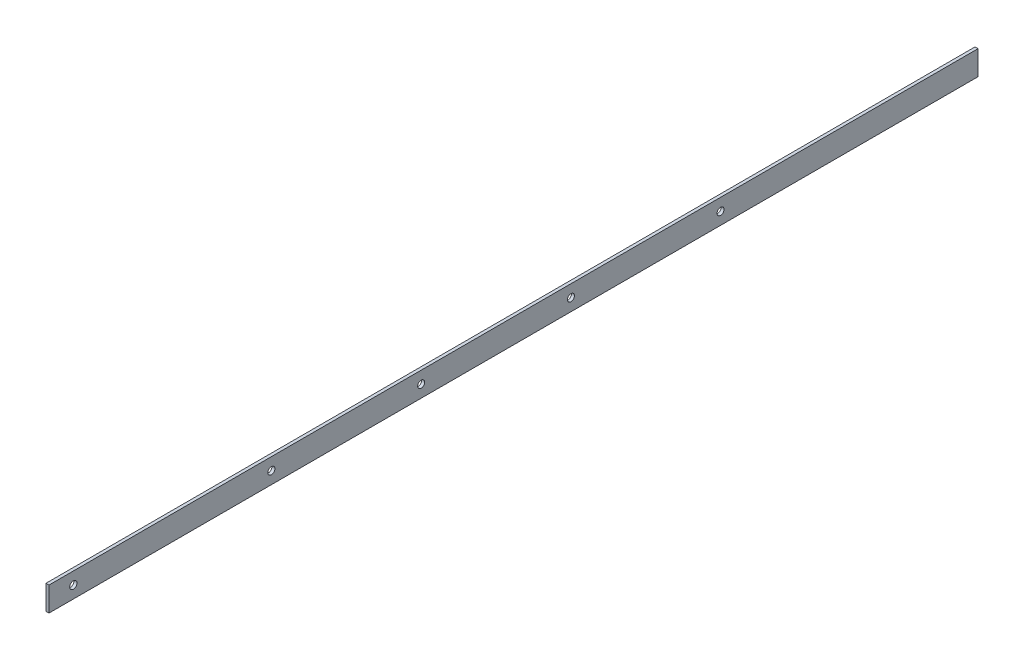
SolidWorks part; units mm, degrees
ref_plane "Front Plane" through (0, 0, 0) normal (0, 0, 1) x (1, 0, 0)
ref_plane "Top Plane" through (0, 0, 0) normal (0, 1, 0) x (1, 0, 0)
ref_plane "Right Plane" through (0, 0, 0) normal (1, 0, 0) x (0, 0, -1)
sketch "Sketch1" plane through (0, 0, 0) normal (0, 0, 1) x (1, 0, 0)
  line L1 (0, 0) -> (1.5875, 0)
  line L2 (0, 0) -> (0, 12.7)
  line L3 (0, 12.7) -> (1.5875, 12.7)
  line L4 (1.5875, 0) -> (1.5875, 12.7)
  dimension "D1" = 1.5875
  dimension "D2" = 12.7
extrude "Boss-Extrude1" add sketch "Sketch1" along normal blind 485.14
hole_wizard "#6 Clearance Hole1" positions "Sketch5" profile "Sketch4" hole size "#6" standard "ANSI Inch" end condition through all
sketch "Sketch5" plane through (1.5875, 0, 0) normal (1, 0, 0) x (0, 0, -1)
  line L0 (-485.14, 0) -> (-485.14, 12.7) construction
  line L1 (-485.14, 12.7) -> (0, 12.7) construction
  point P0 (-472.44, 6.35)
  dimension "D1" = 12.7
  dimension "D2" = 6.35
sketch "Sketch4" plane through (1.5875, 6.35, 472.44) normal (0, 1, 0) x (0, 0, -1)
  line L0 (0, 0) -> (0, 1.5875)
  line L1 (0, 1.5875) -> (1.8986, 1.5875)
  line L2 (1.8986, 1.5875) -> (1.8986, 0)
  line L5 (1.8986, 0) -> (0, 0)
  line L11 (0, -6.35) -> (0, 107.95) construction
  dimension "Thru Hole Dia." = 3.7973
  dimension "Thru Hole Depth" = 1.5875
hole_wizard "#6 Clearance Hole2" positions "Sketch6" profile "Sketch7" hole size "#6" standard "ANSI Inch" end condition through all
sketch "Sketch6" plane through (7.1437, -24.6313, -47.6504) normal (1, 0, 0) x (0, 0, -1)
  point P0 (-416.6839, 30.9813)
  point P3 (-338.4519, 30.9813)
  point P6 (-260.2199, 30.9813)
  point P9 (-182.0811, 30.9813)
sketch "Sketch7" plane through (7.1437, 6.35, 369.0334) normal (0, 1, 0) x (0, 0, -1)
  line L0 (0, 0) -> (0, 7.1437)
  line L1 (0, 7.1437) -> (1.8288, 7.1437)
  line L2 (1.8288, 7.1437) -> (1.8288, 0)
  line L3 (1.8288, 0) -> (0, 0)
  line L4 (0, -6.35) -> (0, 107.95) construction
  dimension "Thru Hole Dia." = 3.6576
  dimension "Thru Hole Depth" = 7.1437
